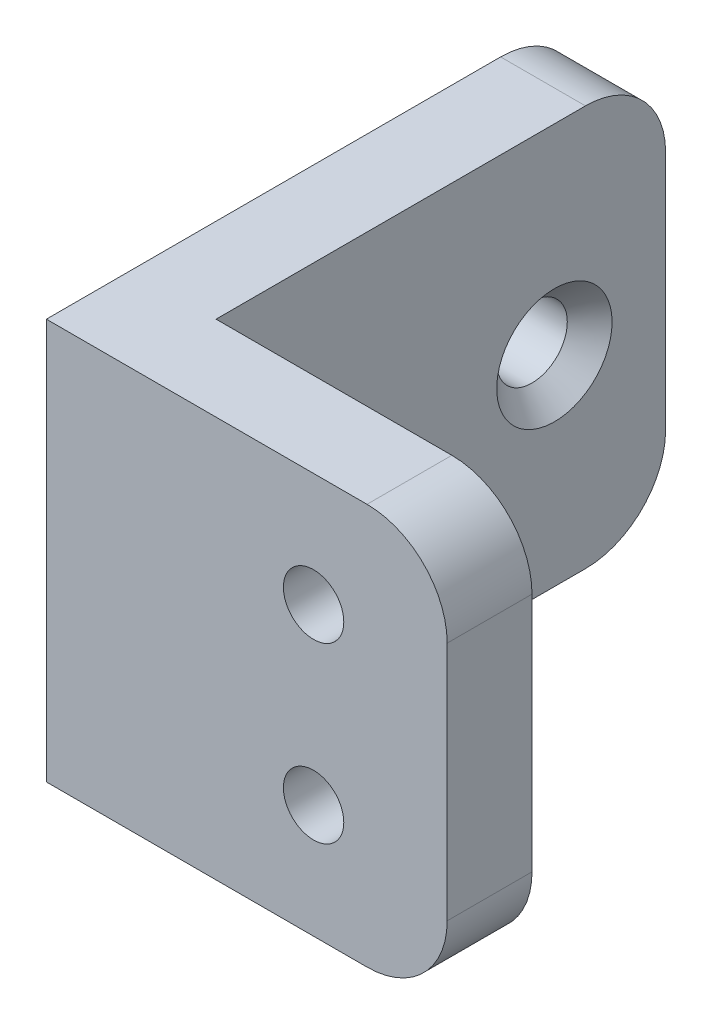
SolidWorks part; units mm, degrees
material "ABS"
ref_plane "Front" through (0, 0, 0) normal (0, 0, 1) x (1, 0, 0)
ref_plane "Top" through (0, 0, 0) normal (0, 1, 0) x (1, 0, 0)
ref_plane "Right" through (0, 0, 0) normal (1, 0, 0) x (0, 0, -1)
sketch "Sketch3" plane through (0, 0, 0) normal (0, 1, 0) x (1, 0, 0)
  line L0 (0, 0) -> (0, 20)
  line L1 (0, 20) -> (3.175, 20)
  line L2 (3.175, 20) -> (3.175, 3.175)
  line L3 (3.175, 3.175) -> (15, 3.175)
  line L4 (15, 3.175) -> (15, 0)
  line L5 (15, 0) -> (0, 0)
  point P3 (8.2721, 3.175)
  dimension "D1" = 15
  dimension "D2" = 20
  dimension "D3" = 3.175
extrude "Boss-Extrude1" add sketch "Sketch3" along normal mid plane 15
hole_wizard "#2 Clearance Hole1" positions "Sketch4" profile "Sketch5" hole size "#2" standard "ANSI Inch" end condition through all
sketch "Sketch4" plane through (0, 0, 0) normal (0, 0, 1) x (1, 0, 0)
  line L0 (10, 3.25) -> (10, -3.25) construction
  line L4 (15, 7.5) -> (15, -7.5) construction
  line L5 (10, 0) -> (15, 0) construction
  point P0 (10, -3.25)
  point P2 (10, 3.25)
  dimension "D1" = 5
  dimension "D2" = 6.5
sketch "Sketch5" plane through (10, -3.25, 0) normal (1, 0, 0) x (0, -1, 0)
  line L0 (0, 0) -> (0, 20)
  line L1 (0, 20) -> (1.1303, 20)
  line L2 (1.1303, 20) -> (1.1303, 0)
  line L5 (1.1303, 0) -> (0, 0)
  line L11 (0, -6.35) -> (0, 107.95) construction
  dimension "Thru Hole Dia." = 2.2606
  dimension "Thru Hole Depth" = 20
hole_wizard "#3 Clearance Hole1" positions "Sketch6" profile "Sketch7" hole size "#3" standard "ANSI Inch" end condition through all
sketch "Sketch6" plane through (3.175, 0, 0) normal (1, 0, 0) x (0, 0, -1)
  line L0 (7.3375, 0) -> (15.8375, 0) construction
  line L2 (11.5875, 0) -> (11.5875, 7.5) construction
  line L3 (3.175, 7.5) -> (20, 7.5) construction
  line L5 (11.5875, 0) -> (11.5875, -7.5) construction
  line L6 (3.175, -7.5) -> (20, -7.5) construction
  point P0 (7.3375, 0)
  point P2 (15.8375, 0)
  dimension "D1" = 8.5
sketch "Sketch7" plane through (3.175, 0, -7.3375) normal (0, 1, 0) x (0, 0, -1)
  line L0 (0, 0) -> (0, 3.175)
  line L1 (0, 3.175) -> (1.3208, 3.175)
  line L2 (1.3208, 3.175) -> (1.3208, 0.8382)
  line L3 (1.3208, 0.8382) -> (2.159, 0)
  line L5 (2.159, 0) -> (0, 0)
  line L6 (-1.3208, 0.8382) -> (-2.159, 0) construction
  line L11 (0, -6.35) -> (0, 107.95) construction
  dimension "Thru Hole Dia." = 2.6416
  dimension "Thru Hole Depth" = 3.175
  dimension "Near C'Sink Dia." = 4.318
  dimension "Near C'Sink Angle" = 90
fillet "Fillet1" radius 3 4 edges at (1.5875, -7.5, -20) (1.5875, 7.5, -20) (15, -7.5, -1.5875) (15, 7.5, -1.5875)
